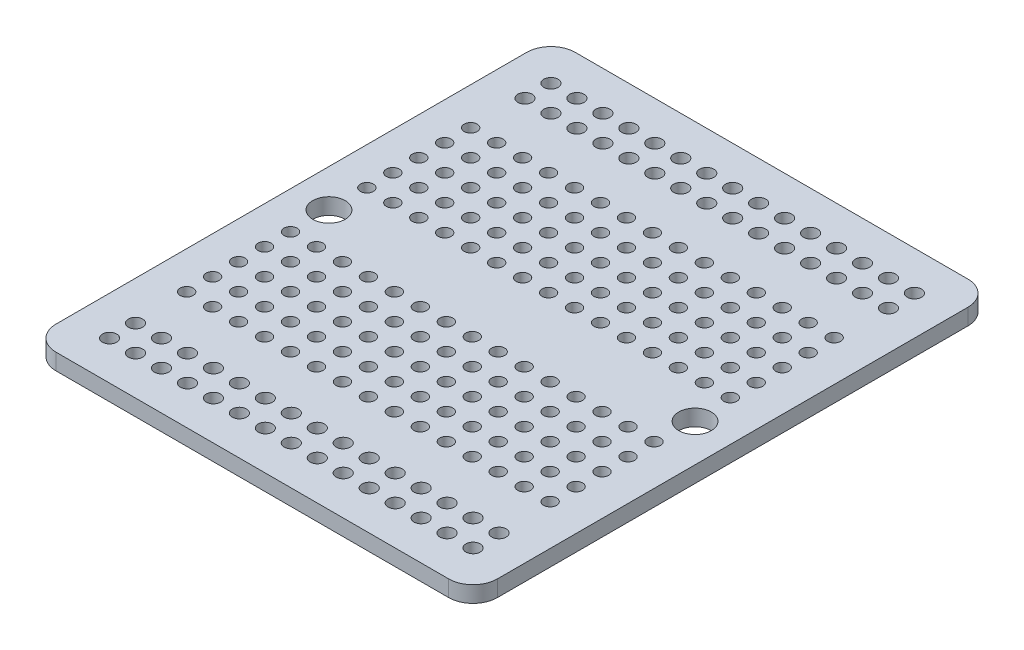
SolidWorks part; units mm, degrees
material "PBT General Purpose"
ref_plane "Front" through (0, 0, 0) normal (0, 0, 1) x (1, 0, 0)
ref_plane "Top" through (0, 0, 0) normal (0, 1, 0) x (1, 0, 0)
ref_plane "Right" through (0, 0, 0) normal (1, 0, 0) x (0, 0, -1)
sketch "Sketch3"
sketch "Sketch1" plane through (0, 0, 0) normal (0, 1, 0) x (1, 0, 0)
  line L1 (-21.59, -25.4) -> (21.59, -25.4)
  line L2 (-21.59, -25.4) -> (-21.59, 25.4)
  line L3 (-21.59, 25.4) -> (21.59, 25.4)
  line L4 (21.59, -25.4) -> (21.59, 25.4)
  line L5 (-21.59, -25.4) -> (21.59, 25.4) construction
  line L6 (-21.59, 25.4) -> (21.59, -25.4) construction
  point P0 (0, 0)
  dimension "D1" = 50.8
  dimension "D2" = 43.18
extrude "Boss-Extrude1" add sketch "Sketch1" along normal blind 1.5875
fillet "Fillet1" radius 2.3813 4 edges at (-21.59, 0.7937, 25.4) (-21.59, 0.7937, -25.4) (21.59, 0.7937, -25.4) (21.59, 0.7937, 25.4)
sketch "Sketch4" plane through (0, 1.5875, 0) normal (0, 1, 0) x (1, 0, 0)
  circle A0 centre (-17.78, 21.59) radius 0.6985
  dimension "D1" = 1.397
  dimension "D2" = 17.78
  dimension "D3" = 21.59
extrude "Cut-Extrude1" cut sketch "Sketch4" against normal through all
pattern_linear "LPattern1" count 15 spacing 2.54 along (1, 0, 0) count 2 spacing 2.54 along (0, 0, 1) of "Cut-Extrude1"
sketch "Sketch5" plane through (0, 0, 0) normal (0, 1, 0) x (1, 0, 0)
  circle A0 centre (-17.9351, 13.8933) radius 0.635
extrude "Cut-Extrude6" cut sketch "Sketch5" along normal through all
pattern_linear "LPattern2" count 15 spacing 2.54 along (1, 0, 0) count 5 spacing 2.54 along (0, 0, 1) of "Cut-Extrude6"
mirror "Mirror1" about plane through (0, 0, 0) normal (0, 0, 1) of "LPattern2", "Cut-Extrude6", "LPattern1", "Cut-Extrude1"
sketch "Sketch6" plane through (0, 1.5875, 0) normal (0, 1, 0) x (1, 0, 0)
  circle A0 centre (-17.907, 0) radius 1.5875
extrude "Cut-Extrude7" cut sketch "Sketch6" against normal through all
mirror "Mirror2" about plane through (0, 0, 0) normal (1, 0, 0) of "Cut-Extrude7"
